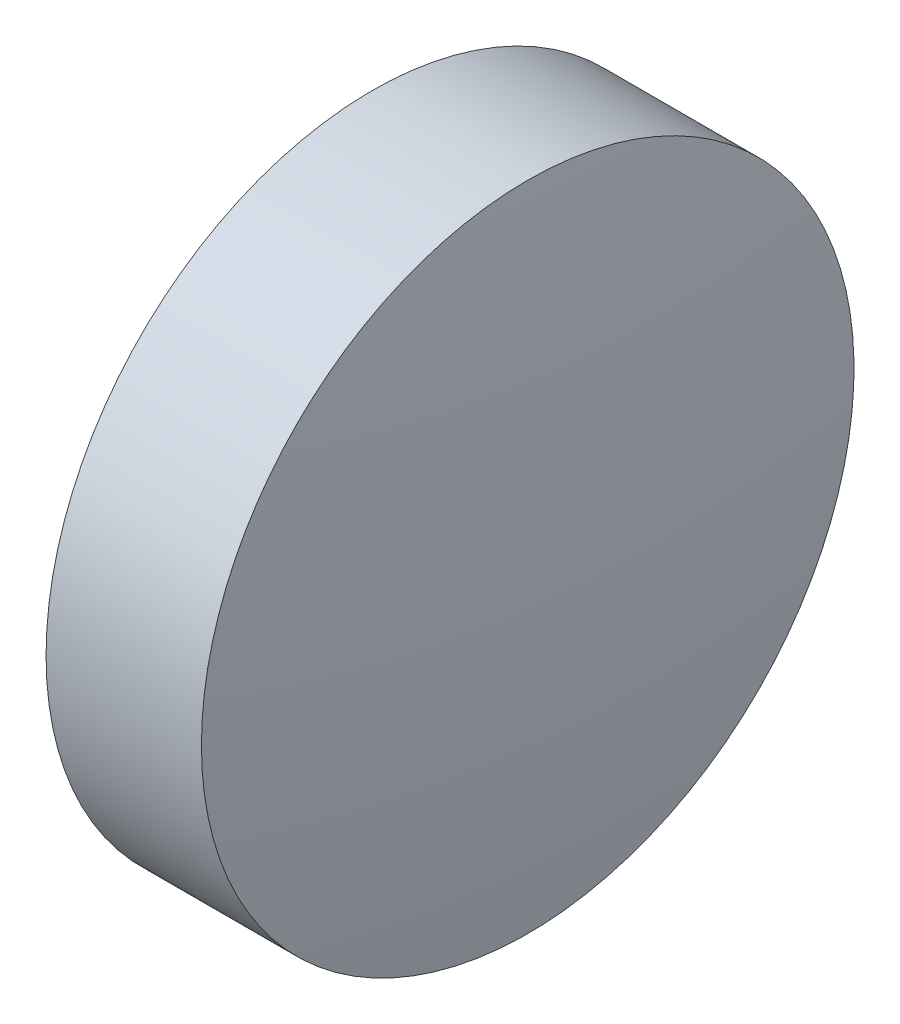
SolidWorks part; units mm, degrees
ref_plane "前视基准面" through (0, 0, 0) normal (0, 0, 1) x (1, 0, 0)
ref_plane "上视基准面" through (0, 0, 0) normal (0, 1, 0) x (1, 0, 0)
ref_plane "右视基准面" through (0, 0, 0) normal (1, 0, 0) x (0, 0, -1)
sketch "草图1" plane through (0, 0, 0) normal (0, 0, 1) x (1, 0, 0)
  line L0 (400.4647, 121.0526) -> (405.8597, 121.0526) construction
  line L1 (401.3253, 121.0526) -> (401.3253, 124.2026)
  line L2 (401.3253, 124.2026) -> (402.8253, 124.2026)
  line L3 (403.0453, 121.0526) -> (401.3253, 121.0526)
  arc A0 (403.0453, 121.0526) -> (402.8253, 124.2026) centre (380.3842, 121.0526) ccw
revolve "旋转1" add sketch "草图1" angle 360 about L0
